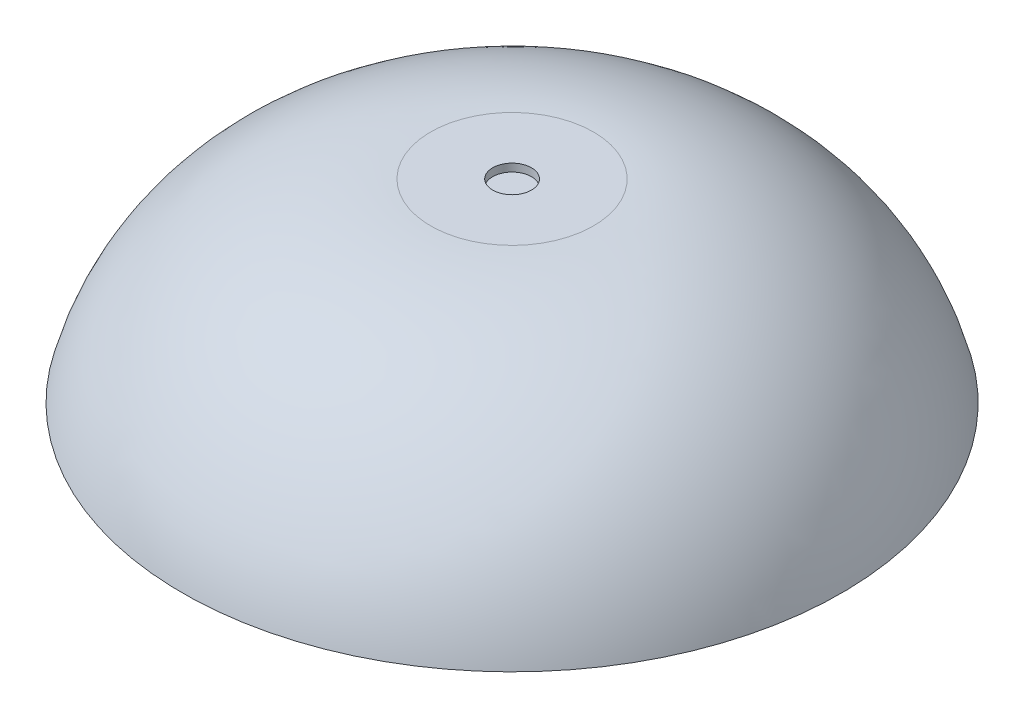
SolidWorks part; units mm, degrees
ref_plane "Alzado" through (0, 0, 0) normal (0, 0, 1) x (1, 0, 0)
ref_plane "Planta" through (0, 0, 0) normal (0, 1, 0) x (1, 0, 0)
ref_plane "Vista lateral" through (0, 0, 0) normal (1, 0, 0) x (0, 0, -1)
sketch "Croquis1" plane through (0, 0, 0) normal (0, 0, 1) x (1, 0, 0)
  line L0 (0, 0) -> (85, 0)
  line L1 (5, 50) -> (21, 50)
  line L2 (5, 48) -> (21, 48)
  line L3 (0, 2) -> (82.3866, 2)
  line L4 (0, 0) -> (0, 2)
  line L6 (5, 50) -> (5, 48)
  line L7 (0, 50) -> (21, 50) construction
  line L8 (0, 48) -> (21, 48) construction
  arc A0 (21, 50) -> (85, 0) centre (21, -15.96) cw
  arc A1 (21, 48) -> (82.3866, 2) centre (21, -15.96) cw
  dimension "D4" = 2
  dimension "D5" = 65.96
  dimension "D1" = 50
  dimension "D2" = 85
  dimension "D3" = 5
revolve "Revolución1" add sketch "Croquis1" angle 360 about L4
